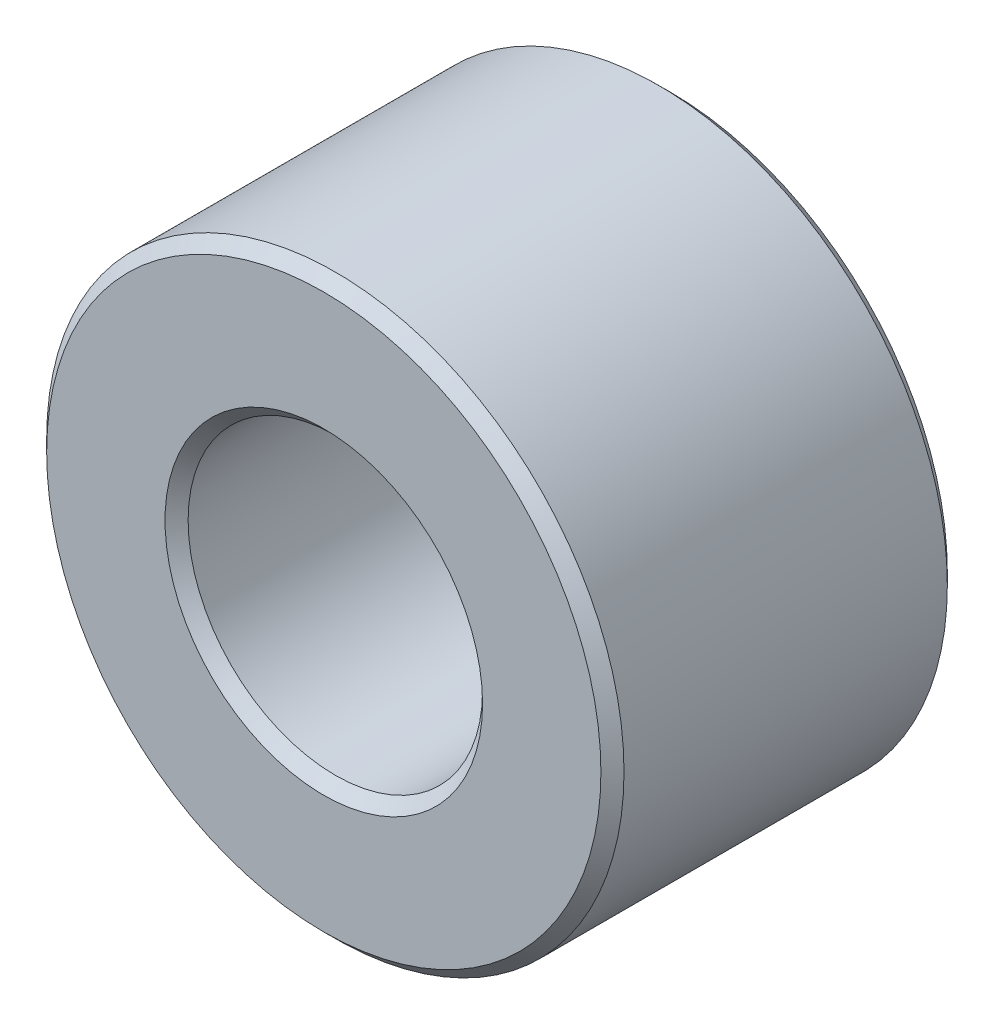
SolidWorks part; units mm, degrees
material "6061-T6 (SS)"
ref_plane "Front Plane" through (0, 0, 0) normal (0, 0, 1) x (1, 0, 0)
ref_plane "Top Plane" through (0, 0, 0) normal (0, 1, 0) x (1, 0, 0)
ref_plane "Right Plane" through (0, 0, 0) normal (1, 0, 0) x (0, 0, -1)
sketch "Sketch1" plane through (0, 0, 0) normal (0, 0, 1) x (1, 0, 0)
  circle A0 centre (0, 0) radius 2.55
  circle A1 centre (0, 0) radius 5
  dimension "D1" = 5.1
  dimension "D2" = 10
extrude "Boss-Extrude1" add sketch "Sketch1" along normal blind 6
chamfer "Chamfer1" distance 0.2 angle 45 4 edges at (5, 0, 0) (2.55, 0, 0) (2.55, 0, 6) (5, 0, 6)
